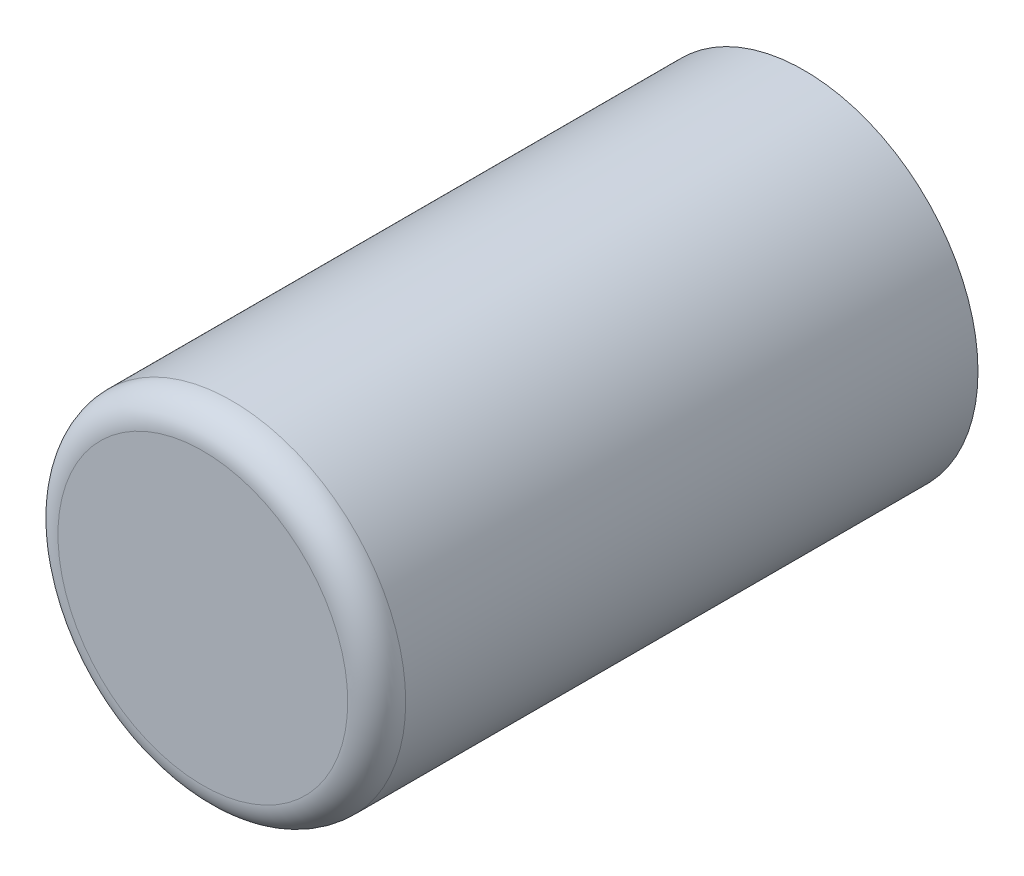
SolidWorks part; units mm, degrees
ref_plane "正面" through (0, 0, 0) normal (0, 0, 1) x (1, 0, 0)
ref_plane "平面" through (0, 0, 0) normal (0, 1, 0) x (1, 0, 0)
ref_plane "右側面" through (0, 0, 0) normal (1, 0, 0) x (0, 0, -1)
sketch "ｽｹｯﾁ1" plane through (0, 0, 0) normal (0, 0, 1) x (1, 0, 0)
  circle A0 centre (0, 0) radius 24
  dimension "D1" = 48
extrude "ﾎﾞｽ - 押し出し1" add sketch "ｽｹｯﾁ1" along normal blind 83
fillet "ﾌｨﾚｯﾄ1" radius 4 1 edges at (24, 0, 83)
shell "ｼｪﾙ1" thickness 0.5
